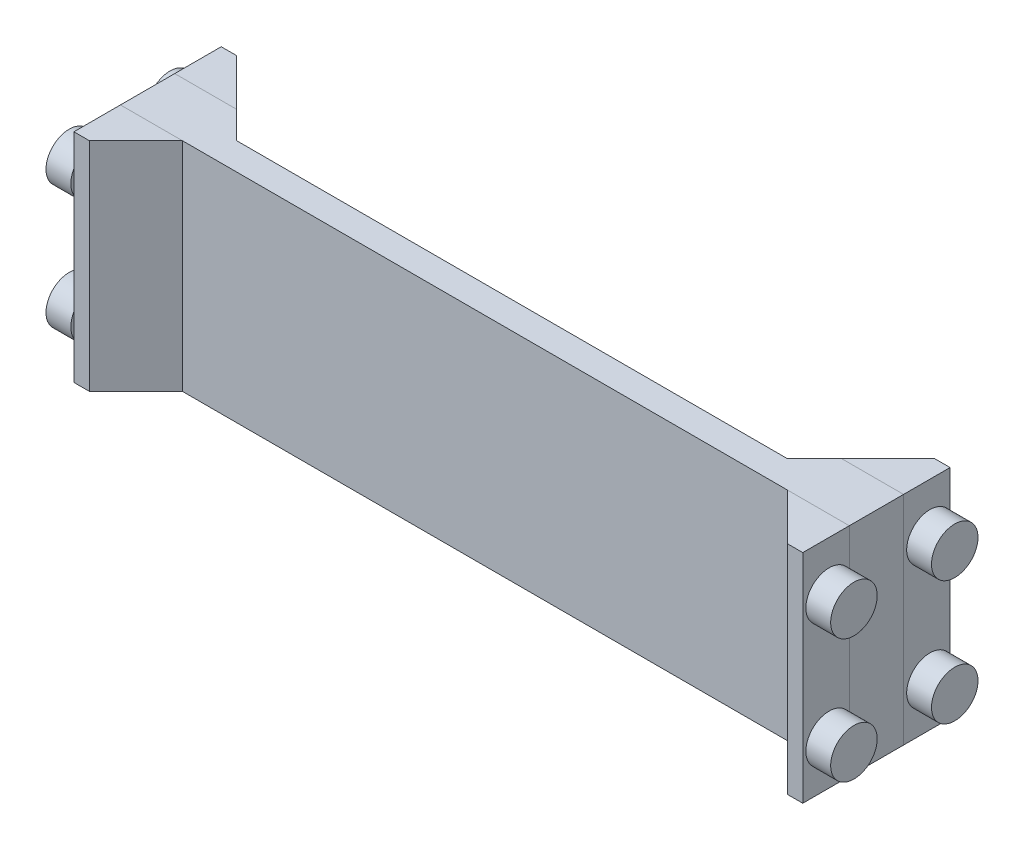
SolidWorks part; units mm, degrees
ref_plane "Front Plane" through (0, 0, 0) normal (0, 0, 1) x (1, 0, 0)
ref_plane "Top Plane" through (0, 0, 0) normal (0, 1, 0) x (1, 0, 0)
ref_plane "Right Plane" through (0, 0, 0) normal (1, 0, 0) x (0, 0, -1)
sketch "Sketch1" plane through (0, 0, 0) normal (0, 0, 1) x (1, 0, 0)
  line L1 (-86.6847, 38.5754) -> (510.2153, 38.5754)
  line L2 (-86.6847, 38.5754) -> (-86.6847, -139.2246)
  line L3 (-86.6847, -139.2246) -> (510.2153, -139.2246)
  line L4 (510.2153, 38.5754) -> (510.2153, -139.2246)
  dimension "D1" = 596.9
  dimension "D2" = 177.8
extrude "Boss-Extrude1" add sketch "Sketch1" along normal blind 44.45
sketch "Sketch2" plane through (0, 38.5754, 0) normal (0, 1, 0) x (1, 0, 0)
  line L2 (497.5153, -82.55) -> (510.2153, -82.55)
  line L3 (510.2153, -82.55) -> (510.2153, -44.45)
  line L4 (510.2153, -44.45) -> (-86.6847, -44.45) construction
  line L5 (497.5153, -82.55) -> (459.4153, -44.45)
  line L9 (510.2153, 0) -> (-86.6847, 0)
  line L10 (-86.6847, 0) -> (-86.6847, -44.45)
  line L11 (-86.6847, -44.45) -> (510.2153, -44.45)
  line L12 (510.2153, -44.45) -> (510.2153, 0)
  line L15 (459.4153, -44.45) -> (510.2153, -44.45)
  line L21 (459.4153, 0) -> (510.2153, 0)
  line L22 (497.5153, 38.1) -> (459.4153, 0)
  line L23 (497.5153, 38.1) -> (510.2153, 38.1)
  line L24 (510.2153, 38.1) -> (510.2153, 0)
  line L26 (-86.6847, 38.1) -> (-86.6847, 0)
  line L27 (-73.9847, 38.1) -> (-86.6847, 38.1)
  line L28 (-73.9847, 38.1) -> (-35.8847, 0)
  line L29 (-35.8847, 0) -> (-86.6847, 0)
  line L30 (-35.8847, -44.45) -> (-86.6847, -44.45)
  line L31 (-73.9847, -82.55) -> (-35.8847, -44.45)
  line L32 (-86.6847, -82.55) -> (-86.6847, -44.45)
  line L33 (-73.9847, -82.55) -> (-86.6847, -82.55)
  dimension "D1" = 38.1
  dimension "D2" = 12.7
  dimension "D3" = 0
extrude "Boss-Extrude2" add sketch "Sketch2" against normal blind 177.8 separate body
sketch "Sketch3" plane through (510.2153, 0, 0) normal (1, 0, 0) x (0, 0, -1)
  line L0 (-44.45, -139.2246) -> (-44.45, 38.5754) construction
  line L3 (-82.55, 38.5754) -> (-44.45, 38.5754) construction
  circle A0 centre (-63.5, 0.4754) radius 12.7
  circle A1 centre (19.05, 0.4754) radius 12.7
  circle A2 centre (-63.5, -101.1246) radius 12.7
  circle A3 centre (19.05, -101.1246) radius 12.7
  dimension "D1" = 19.05
  dimension "D2" = 38.1
extrude "Boss-Extrude3" add sketch "Sketch3" along normal blind 2.54
sketch "Sketch4" plane through (512.7553, 0, 0) normal (1, 0, 0) x (0, 0, -1)
  circle A0 centre (-63.5, 0.4754) radius 19.05
extrude "Boss-Extrude4" add sketch "Sketch4" along normal blind 20.32
sketch "Sketch5" plane through (512.7553, 0, 0) normal (1, 0, 0) x (0, 0, -1)
  circle A0 centre (19.05, 0.4754) radius 19.05
extrude "Boss-Extrude5" add sketch "Sketch5" along normal blind 20.32
sketch "Sketch6" plane through (512.7553, 0, 0) normal (1, 0, 0) x (0, 0, -1)
  circle A0 centre (19.05, -101.1246) radius 19.05
extrude "Boss-Extrude6" add sketch "Sketch6" along normal blind 20.32
sketch "Sketch7" plane through (512.7553, 0, 0) normal (1, 0, 0) x (0, 0, -1)
  circle A0 centre (-63.5, -101.1246) radius 19.05
extrude "Boss-Extrude7" add sketch "Sketch7" along normal blind 20.32
sketch "Sketch8" plane through (-86.6847, 0, 0) normal (-1, 0, 0) x (0, 0, 1)
  line L0 (-38.1, -139.2246) -> (0, -139.2246) construction
  line L1 (-38.1, -139.2246) -> (-38.1, 38.5754) construction
  circle A0 centre (-19.05, -101.1246) radius 12.7
  circle A1 centre (-19.05, 0.4754) radius 12.7
  circle A2 centre (63.5, 0.4754) radius 12.7
  circle A3 centre (63.5, -101.1246) radius 12.7
  dimension "D1" = 38.1
  dimension "D2" = 19.05
extrude "Boss-Extrude8" add sketch "Sketch8" along normal blind 2.54
sketch "Sketch9" plane through (-89.2247, 0, 0) normal (-1, 0, 0) x (0, 0, 1)
  circle A0 centre (63.5, -101.1246) radius 19.05
extrude "Boss-Extrude9" add sketch "Sketch9" along normal blind 20.32
sketch "Sketch10" plane through (-89.2247, 0, 0) normal (-1, 0, 0) x (0, 0, 1)
  circle A0 centre (63.5, 0.4754) radius 19.05
extrude "Boss-Extrude10" add sketch "Sketch10" along normal blind 20.32
sketch "Sketch11" plane through (-89.2247, 0, 0) normal (-1, 0, 0) x (0, 0, 1)
  circle A0 centre (-19.05, -101.1246) radius 19.05
extrude "Boss-Extrude11" add sketch "Sketch11" along normal blind 20.32
sketch "Sketch12" plane through (-89.2247, 0, 0) normal (-1, 0, 0) x (0, 0, 1)
  circle A0 centre (-19.05, 0.4754) radius 19.05
extrude "Boss-Extrude12" add sketch "Sketch12" along normal blind 20.32
sketch "Sketch13" plane through (0, -139.2246, 0) normal (0, -1, 0) x (1, 0, 0)
  line L0 (459.4153, 0) -> (-35.8847, 0)
  line L4 (459.4153, 0) -> (437.1903, 22.225)
  line L5 (-35.8847, 0) -> (-13.6597, 22.225)
  line L6 (437.1903, 22.225) -> (-13.6597, 22.225)
extrude "Cut-Extrude1" cut sketch "Sketch13" against normal blind 304.8
